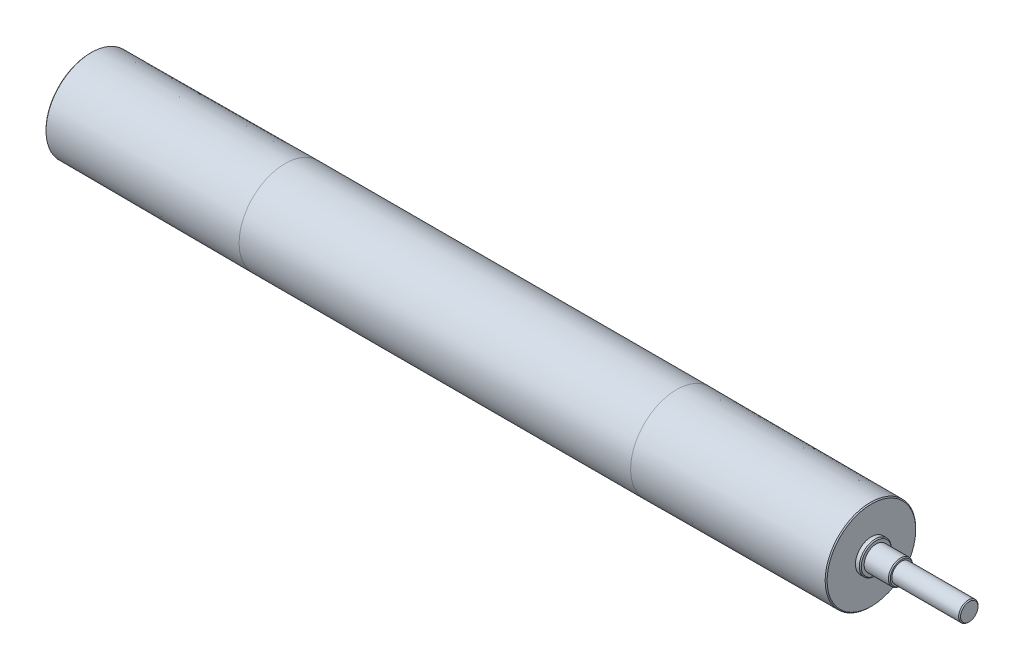
SolidWorks part; units mm, degrees
material "6061 Alloy"
ref_plane "Front" through (0, 0, 0) normal (0, 0, 1) x (1, 0, 0)
ref_plane "Top" through (0, 0, 0) normal (0, 1, 0) x (1, 0, 0)
ref_plane "Right" through (0, 0, 0) normal (1, 0, 0) x (0, 0, -1)
sketch "Sketch1" plane through (0, 0, 0) normal (0, 0, 1) x (1, 0, 0)
  line L0 (-202, -47.5) -> (202, -47.5)
  line L1 (0, 0) -> (0, -47.5) construction
  line L2 (-202, -47.5) -> (-402, -46.75)
  line L3 (202, -47.5) -> (402, -46.75)
  line L4 (402, -46.75) -> (403, -45.7425)
  line L5 (-402, -46.75) -> (-403, -45.75)
  line L6 (403, -45.7425) -> (403, -16.5)
  line L7 (-403, -45.75) -> (-403, -16.5)
  line L8 (-403, -16.5) -> (-407, -16.5)
  line L9 (-407, -16.5) -> (-408, -15.5)
  line L10 (-408, -15.5) -> (-408, -12.5)
  line L11 (-408, -12.5) -> (-425, -12.5)
  line L12 (-425, -12.5) -> (-426, -11.5)
  line L13 (-426, -11.5) -> (-426, 0)
  line L14 (-426, 0) -> (504, 0)
  line L15 (403, -16.5) -> (407, -16.5)
  line L16 (407, -16.5) -> (408, -15.5)
  line L17 (408, -15.5) -> (408, -12.5)
  line L18 (434, -10) -> (503, -10)
  line L19 (504, -9) -> (504, 0)
  line L20 (503, -10) -> (504, -9)
  line L21 (408, -12.5) -> (433, -12.5)
  line L22 (433, -12.5) -> (434, -11.5)
  line L23 (434, -11.5) -> (434, -10)
  dimension "D1" = 47.5
  dimension "D2" = 200
  dimension "D3" = 200
  dimension "D4" = 46.75
  dimension "D5" = 1
  dimension "D6" = 135
  dimension "D7" = 1
  dimension "D8" = 1
  dimension "D9" = 16.5
  dimension "D10" = 16.5
  dimension "D11" = 135
  dimension "D12" = 1
  dimension "D13" = 5
  dimension "D14" = 12.5
  dimension "D15" = 1
  dimension "D16" = 135
  dimension "D17" = 18
  dimension "D18" = 5
  dimension "D19" = 1
  dimension "D20" = 135
  dimension "D21" = 10
  dimension "D22" = 26
  dimension "D23" = 135
  dimension "D24" = 1
  dimension "D25" = 806
  dimension "D26" = 12.5
  dimension "D27" = 1
  dimension "D28" = 135
  dimension "D29" = 70
revolve "Revolve1" add sketch "Sketch1" angle 360 about L14
ref_plane "Plane1" through (468.5, 0, -10) normal (0, 0, -1) x (0, -1, 0)
sketch "Sketch2" plane through (468.5, 0, -10) normal (0, 0, -1) x (0, -1, 0)
  line L0 (-3, 16.5) -> (-3, -27.5)
  line L1 (3, 16.5) -> (3, -27.5)
  line L2 (-10, -34.5) -> (10, -34.5) construction
  line L3 (-10, -34.5) -> (10, -34.5)
  line L4 (0, -34.5) -> (0, -45.8085) construction
  line L5 (0, -30.5) -> (-16.3213, -30.5) construction
  line L6 (-9, -35.5) -> (9, -35.5) construction
  line L7 (0, 19.5) -> (-16.3213, 19.5) construction
  arc A0 (3, 16.5) -> (-3, 16.5) centre (0, 16.5) ccw
  arc A1 (-3, -27.5) -> (3, -27.5) centre (0, -27.5) ccw
  dimension "D1" = 3
  dimension "D2" = 3
  dimension "D3" = 5
  dimension "D4" = 50
extrude "Extrude1" cut sketch "Sketch2" against normal blind 3.5 contours L0 A1 L1 A0
